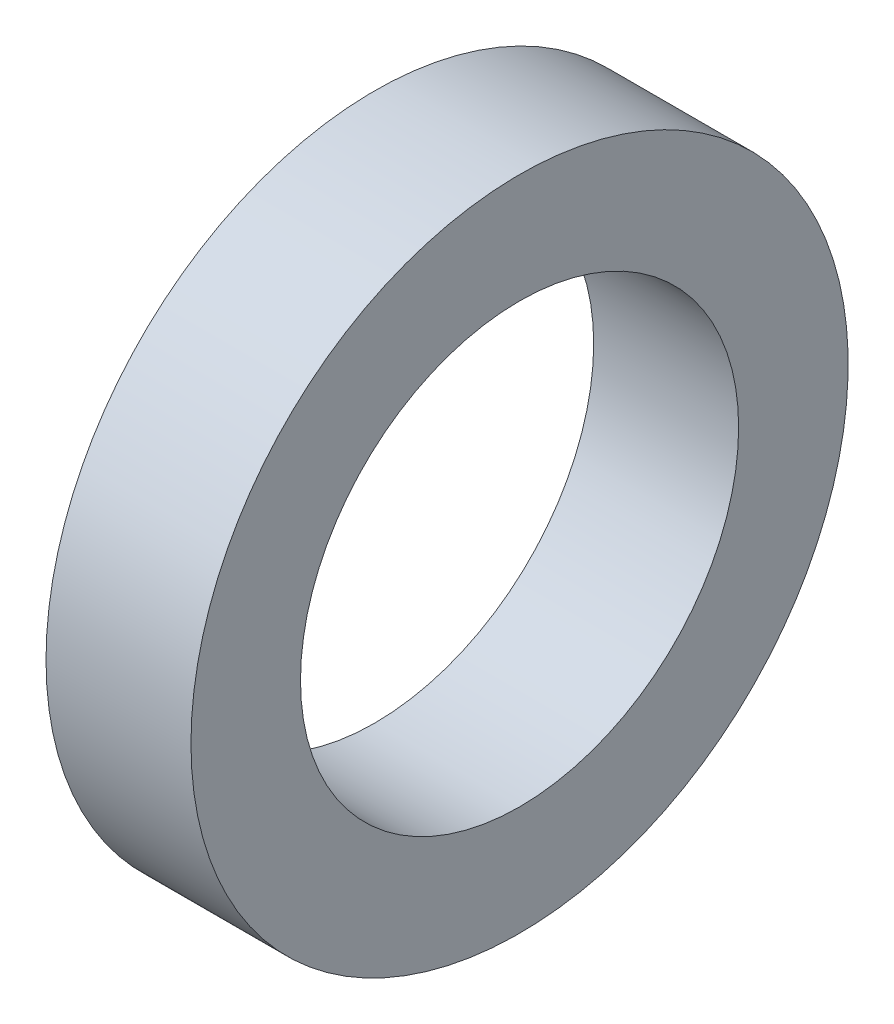
SolidWorks part; units mm, degrees
ref_plane "Front Plane" through (0, 0, 0) normal (0, 0, 1) x (1, 0, 0)
ref_plane "Top Plane" through (0, 0, 0) normal (0, 1, 0) x (1, 0, 0)
ref_plane "Right Plane" through (0, 0, 0) normal (1, 0, 0) x (0, 0, -1)
sketch "Sketch2" plane through (0, 0, 0) normal (0, 0, 1) x (1, 0, 0)
  line L0 (0, 0) -> (58.591, 0) construction
  line L2 (0, 0) -> (18.4, 0)
  line L3 (0, 0) -> (0, 2.5)
  line L4 (0, 2.5) -> (18.4, 2.5)
  line L5 (18.4, 0) -> (18.4, 2.5)
  line L6 (6.0094, 2.5) -> (6.0094, 6)
  line L11 (6.0094, 6) -> (9.9794, 6)
  line L16 (12.9794, 6) -> (12.9794, 3)
  line L17 (12.9794, 3) -> (13.6398, 3)
  line L18 (13.6398, 3) -> (13.6398, 2.5)
  line L19 (13.6398, 2.5) -> (6.0094, 2.5)
  line L22 (13.6398, 2.5) -> (16.1198, 2.5)
  line L23 (13.6398, 2.5) -> (13.6398, 4)
  line L24 (13.6398, 4) -> (16.1198, 4)
  line L25 (16.1198, 2.5) -> (16.1198, 4)
  line L27 (6.0094, 6) -> (9.9794, 6)
  line L28 (6.0094, 6) -> (6.0094, 9)
  line L29 (6.0094, 9) -> (9.9794, 9)
  line L30 (9.9794, 6) -> (9.9794, 9)
  line L31 (6.0094, 9) -> (6.0094, 8.25)
  line L32 (6.0094, 8.25) -> (5.0094, 8.25)
  line L33 (8.6609, 22.001) -> (8.6609, 12.476) construction
  line L34 (5.0094, 12.476) -> (12.3124, 12.476)
  line L35 (9.9794, 9) -> (12.3124, 9)
  line L36 (5.0094, 7.9375) -> (1.7709, 7.9375)
  line L37 (5.0094, 8.25) -> (5.0094, 12.476)
  line L38 (5.0094, 7.9375) -> (5.0094, 13.9365)
  line L39 (5.0094, 13.9365) -> (1.7709, 13.9365)
  line L40 (1.7709, 7.9375) -> (1.7709, 13.9365)
  line L41 (5.0094, 22.001) -> (12.3124, 22.001)
  line L42 (5.0094, 22.001) -> (5.0094, 30.1625)
  line L43 (5.0094, 30.1625) -> (12.3124, 30.1625)
  line L44 (12.3124, 22.001) -> (12.3124, 30.1625)
  line L49 (16.6398, 22.001) -> (16.6398, 7.5)
  line L51 (23.0198, 7.5) -> (23.0198, 6.5)
  line L54 (16.1198, 4) -> (13.6398, 4)
  line L56 (18.0398, 7.5) -> (23.0198, 7.5)
  line L57 (13.3124, 22.001) -> (16.6398, 22.001)
  line L58 (16.1198, 3.5) -> (20.0198, 3.5)
  line L59 (29.9098, 14) -> (26.9098, 11)
  line L60 (4.0094, 31.75) -> (18.0398, 31.75)
  line L61 (18.0398, 7.5) -> (23.0198, 7.5)
  line L62 (18.0398, 7.5) -> (18.0398, 12)
  line L63 (18.0398, 12) -> (23.0198, 12)
  line L64 (23.0198, 7.5) -> (23.0198, 12)
  line L65 (18.0398, 31.75) -> (18.0398, 12)
  line L66 (23.0198, 11) -> (26.9098, 11)
  line L67 (34.8098, 23) -> (31.3098, 19.5)
  line L68 (35.8098, 31) -> (38.7998, 33.99)
  line L69 (29.9098, 14) -> (29.9098, 15)
  line L70 (29.9098, 15) -> (22.9398, 15)
  line L71 (22.9398, 15) -> (21.0398, 15)
  line L72 (18.0398, 7.5) -> (16.6398, 7.5)
  line L73 (21.0398, 15) -> (21.0398, 43)
  line L74 (19.6115, 40) -> (9.6516, 40)
  line L75 (9.6516, 40) -> (4.0094, 40)
  line L76 (21.0398, 43) -> (19.6115, 43)
  line L77 (22.9398, 15) -> (29.9098, 15)
  line L78 (22.9398, 15) -> (22.9398, 21)
  line L79 (22.9398, 21) -> (29.9098, 21)
  line L80 (29.9098, 15) -> (29.9098, 21)
  line L81 (9.6516, 40) -> (19.6115, 40)
  line L82 (9.6516, 40) -> (9.6516, 50)
  line L83 (9.6516, 50) -> (19.6115, 50)
  line L84 (19.6115, 40) -> (19.6115, 50)
  line L85 (4.0094, 40) -> (4.0094, 31.75)
  line L86 (12.9794, 3) -> (12.9794, 2.5)
  line L87 (31.3098, 19.5) -> (29.9098, 19.5)
  line L88 (21.4694, 63.5) -> (21.4694, 51.308)
  line L89 (21.4694, 63.5) -> (25.9398, 63.5)
  line L90 (25.9398, 63.5) -> (25.9398, 25)
  line L91 (27.8398, 25) -> (25.9398, 25)
  line L92 (9.6516, 48) -> (8.2233, 48)
  line L93 (8.2233, 48) -> (8.2233, 53.476)
  line L94 (8.2233, 53.476) -> (19.6115, 53.476)
  line L95 (19.6115, 53.476) -> (19.6115, 50)
  line L96 (13.9174, 63.001) -> (13.9174, 53.476) construction
  line L97 (8.2233, 63.001) -> (19.6115, 63.001)
  line L98 (8.2233, 63.001) -> (8.2233, 68.2625)
  line L99 (8.2233, 68.2625) -> (19.6115, 68.2625)
  line L100 (19.6115, 63.001) -> (19.6115, 68.2625)
  line L101 (12.9794, 6) -> (11.9794, 6)
  line L102 (8.2233, 44.825) -> (4.9848, 44.825)
  line L103 (8.2233, 44.825) -> (8.2233, 54.9365)
  line L104 (8.2233, 54.9365) -> (4.9848, 54.9365)
  line L106 (9.9794, 6) -> (10.8794, 6)
  line L107 (27.8398, 25) -> (34.8098, 25)
  line L108 (34.8098, 25) -> (34.8098, 23)
  line L109 (0, 0) -> (-2, 0)
  line L110 (0, 0) -> (0, 11)
  line L111 (27.8398, 25) -> (34.8098, 25)
  line L112 (27.8398, 25) -> (27.8398, 32.5)
  line L113 (27.8398, 32.5) -> (34.8098, 32.5)
  line L114 (34.8098, 25) -> (34.8098, 32.5)
  line L115 (35.8098, 31) -> (34.8098, 31)
  line L116 (27.8398, 32.5) -> (27.8398, 64.5)
  line L117 (20.5849, 74.025) -> (6.2499, 74.025)
  line L118 (6.2499, 74.025) -> (6.2499, 76.2)
  line L119 (38.7998, 47.29) -> (30.8398, 55.25)
  line L120 (0, 11) -> (-2, 11)
  line L121 (38.7998, 43.815) -> (30.8623, 43.815)
  line L123 (-4.8152, 69.85) -> (1.5348, 76.2)
  line L124 (38.7998, 47.29) -> (38.7998, 33.99)
  line L125 (-2, 0) -> (-2, 11)
  line L126 (38.7998, 37.465) -> (30.8623, 37.465)
  line L127 (30.8623, 43.815) -> (30.8623, 37.465)
  line L128 (6.0094, 2.5) -> (6.0094, 0)
  line L129 (-0.0152, 63.5) -> (-0.0152, 30)
  line L132 (4.9848, 63.5) -> (-0.0152, 63.5)
  line L136 (-1.8152, 30) -> (-11.7752, 30)
  line L138 (-13.7752, 25.4) -> (-2, 25.4)
  line L139 (-2, 25.4) -> (-2, 11.5)
  line L140 (27.8398, 64.5) -> (20.5849, 64.5)
  line L141 (-1.8152, 30) -> (-11.7752, 30)
  line L142 (-1.8152, 30) -> (-1.8152, 39)
  line L143 (-1.8152, 39) -> (-11.7752, 39)
  line L144 (-11.7752, 30) -> (-11.7752, 39)
  line L145 (20.5849, 64.5) -> (20.5849, 74.025)
  line L146 (-12.7752, 37) -> (-12.7752, 47.29)
  line L147 (-12.7752, 37) -> (-11.7752, 37)
  line L148 (30.8398, 55.25) -> (30.8398, 76.2)
  line L149 (11.9794, 6) -> (11.9794, 5.45)
  line L154 (-2, 11.5) -> (0.5, 11.5)
  line L155 (4.9848, 60.6197) -> (24.0348, 60.6197)
  line L160 (4.9848, 60.6197) -> (4.9848, 55.8572)
  line L161 (4.9848, 55.8572) -> (24.0348, 55.8572)
  line L166 (24.0348, 60.6197) -> (24.0348, 55.8572)
  line L167 (4.9848, 60.6197) -> (24.0348, 55.8572) construction
  line L172 (4.9848, 55.8572) -> (24.0348, 60.6197) construction
  line L173 (24.0348, 62.2072) -> (25.9398, 62.2072)
  line L174 (11.9794, 5.45) -> (10.8794, 5.45)
  line L175 (10.8794, 6) -> (10.8794, 5.45)
  line L176 (24.0348, 62.2072) -> (24.0348, 54.2697)
  line L177 (24.0348, 54.2697) -> (25.9398, 54.2697)
  line L178 (25.9398, 62.2072) -> (25.9398, 54.2697)
  line L179 (24.0348, 62.2072) -> (25.9398, 54.2697) construction
  line L180 (24.0348, 54.2697) -> (25.9398, 62.2072) construction
  line L181 (3, 19.6197) -> (15.7, 19.6197)
  line L182 (3, 19.6197) -> (3, 14.8572)
  line L183 (3, 14.8572) -> (15.7, 14.8572)
  line L184 (15.7, 19.6197) -> (15.7, 14.8572)
  line L185 (3, 19.6197) -> (15.7, 14.8572) construction
  line L186 (3, 14.8572) -> (15.7, 19.6197) construction
  line L187 (15.7, 21.2072) -> (16.6398, 21.2072)
  line L188 (15.7, 21.2072) -> (15.7, 13.2697)
  line L189 (15.7, 13.2697) -> (16.6398, 13.2697)
  line L190 (16.6398, 21.2072) -> (16.6398, 13.2697)
  line L191 (15.7, 21.2072) -> (16.6398, 13.2697) construction
  line L192 (15.7, 13.2697) -> (16.6398, 21.2072) construction
  line L193 (0.5, 11.5) -> (0.5, 6.9375)
  line L194 (0.5, 6.9375) -> (1.7709, 6.9375)
  line L195 (23.0198, 6.5) -> (20.0198, 3.5)
  line L196 (4.9848, 63.5) -> (4.9848, 54.9365)
  line L197 (3, 43.825) -> (4.9848, 43.825)
  line L198 (1.7709, 6.9375) -> (1.7709, 7.9375)
  line L199 (6.0094, 0) -> (12.9794, 0)
  line L200 (12.9794, 0) -> (12.9794, 2.5)
  line L201 (18.0398, 31.75) -> (18.0398, 35.875)
  line L202 (18.0398, 35.875) -> (21.0398, 35.875)
  line L203 (30.8398, 76.2) -> (6.2499, 76.2)
  line L204 (2.8049, 69.85) -> (7.2499, 69.85) construction
  line L205 (7.2499, 67.4688) -> (26.2999, 67.4688)
  line L206 (7.2499, 74.025) -> (7.2499, 64.5)
  line L207 (7.2499, 64.5) -> (-1.8152, 64.5)
  line L208 (-1.8152, 64.5) -> (-1.8152, 39)
  line L209 (-12.7752, 47.29) -> (-4.8152, 55.25)
  line L210 (-4.8152, 55.25) -> (-4.8152, 69.85)
  line L211 (7.2499, 67.4688) -> (7.2499, 72.2312)
  line L212 (7.2499, 72.2312) -> (26.2999, 72.2313)
  line L213 (26.2999, 67.4688) -> (26.2999, 72.2313)
  line L214 (26.2999, 73.8187) -> (30.8398, 73.8187)
  line L215 (26.2999, 73.8187) -> (26.2999, 65.8813)
  line L216 (26.2999, 65.8813) -> (30.8398, 65.8813)
  line L217 (30.8398, 73.8187) -> (30.8398, 65.8813)
  line L218 (2.8049, 72.2313) -> (25.0299, 72.2313)
  line L219 (2.8049, 72.2313) -> (2.8049, 67.4687)
  line L220 (2.8049, 67.4687) -> (25.0299, 67.4687)
  line L221 (25.0299, 72.2313) -> (25.0299, 67.4687)
  line L222 (25.0299, 69.85) -> (20.5849, 69.85) construction
  line L223 (21.4694, 51.308) -> (22.9398, 51.308)
  line L224 (22.9398, 51.308) -> (22.9398, 21)
  line L225 (13.6398, 4) -> (13.6398, 12.2697)
  line L226 (13.6398, 12.2697) -> (13.3124, 12.2697)
  line L227 (13.3124, 12.2697) -> (13.3124, 22.001)
  line L228 (12.3124, 9) -> (12.3124, 12.476)
  line L229 (-1.8152, 30) -> (-0.0152, 30)
  line L230 (8.2233, 65.6317) -> (2.8049, 65.6317) construction
  line L231 (19.6115, 65.6317) -> (25.0299, 65.6317) construction
  line L232 (1.5348, 76.2) -> (6.2499, 76.2)
  line L233 (-11.7752, 30) -> (-13.7752, 30)
  line L234 (-13.7752, 30) -> (-13.7752, 25.4)
  line L235 (3, 13.9365) -> (3, 43.825)
  line L236 (4.9848, 54.9365) -> (4.9848, 44.825)
  line L237 (4.9848, 43.825) -> (4.9848, 44.825)
  circle A0 centre (26.8898, 25.95) radius 0.95
  circle A1 centre (21.9898, 15.95) radius 0.95
  circle A2 centre (17.3398, 8.2) radius 0.7
  circle A3 centre (10.4294, 6.45) radius 0.45
  circle A4 centre (-0.9152, 30.9) radius 0.9
  point P7 (24.9873, 58.2385)
  point P131 (16.1699, 17.2385)
  point P135 (14.5098, 58.2385)
  point P146 (9.35, 17.2385)
sketch "Sketch3" plane through (0, 0, 0) normal (0, 0, 1) x (1, 0, 0)
  line L0 (6.0094, 9) -> (9.9794, 9) construction
  line L1 (9.9794, 6) -> (9.9794, 9) construction
  line L2 (6.0094, 6) -> (9.9794, 6) construction
  line L3 (6.0094, 6) -> (6.0094, 9) construction
  line L4 (6.0094, 9) -> (9.9794, 9)
  line L5 (9.9794, 6) -> (9.9794, 9)
  line L6 (6.0094, 6) -> (9.9794, 6)
  line L7 (6.0094, 6) -> (6.0094, 9)
revolve "Revolve1" add sketch "Sketch3" angle 360 about L0
